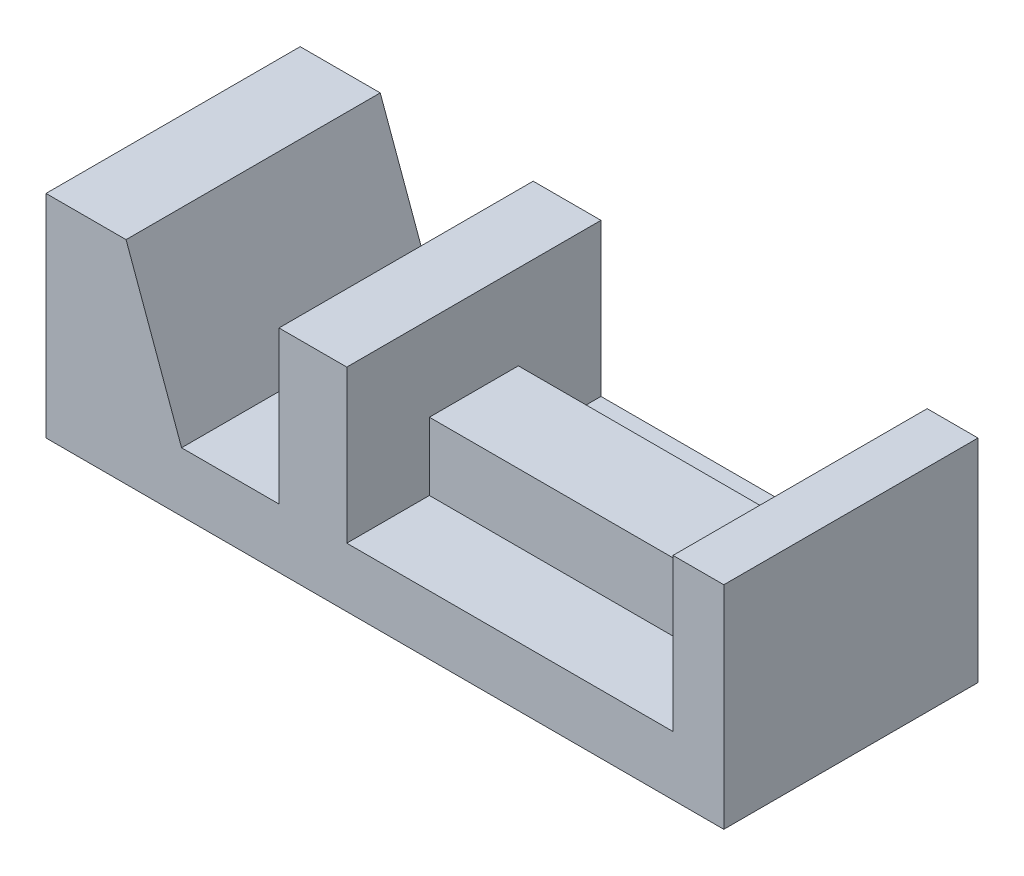
SolidWorks part; units mm, degrees
ref_plane "Front Plane" through (0, 0, 0) normal (0, 0, 1) x (1, 0, 0)
ref_plane "Top Plane" through (0, 0, 0) normal (0, 1, 0) x (1, 0, 0)
ref_plane "Right Plane" through (0, 0, 0) normal (1, 0, 0) x (0, 0, -1)
sketch "Sketch2" plane through (0, 0, 0) normal (0, 0, 1) x (1, 0, 0)
  line L0 (0, 0) -> (0, 50)
  line L1 (0, 0) -> (160, 0)
  line L2 (160, 0) -> (160, 50)
  line L3 (160, 50) -> (148, 50)
  line L4 (148, 50) -> (148, 14)
  line L5 (148, 14) -> (71, 14)
  line L6 (71, 14) -> (71, 50)
  line L7 (71, 50) -> (55, 50)
  line L8 (55, 50) -> (55, 14)
  line L9 (55, 14) -> (32, 14)
  line L10 (32, 14) -> (18.8971, 50)
  line L11 (0, 50) -> (18.8971, 50)
extrude "Boss-Extrude1" add sketch "Sketch2" along normal blind 60
sketch "Sketch3" plane through (0, 14, 0) normal (0, 1, 0) x (1, 0, 0)
  line L1 (71, -60) -> (71, 0) construction
  line L2 (148, -60) -> (148, 0) construction
  line L3 (71, -40.5) -> (148, -40.5)
  line L4 (71, -40.5) -> (71, -19.5)
  line L5 (71, -19.5) -> (148, -19.5)
  line L6 (148, -40.5) -> (148, -19.5)
extrude "Boss-Extrude2" add sketch "Sketch3" along normal blind 16
